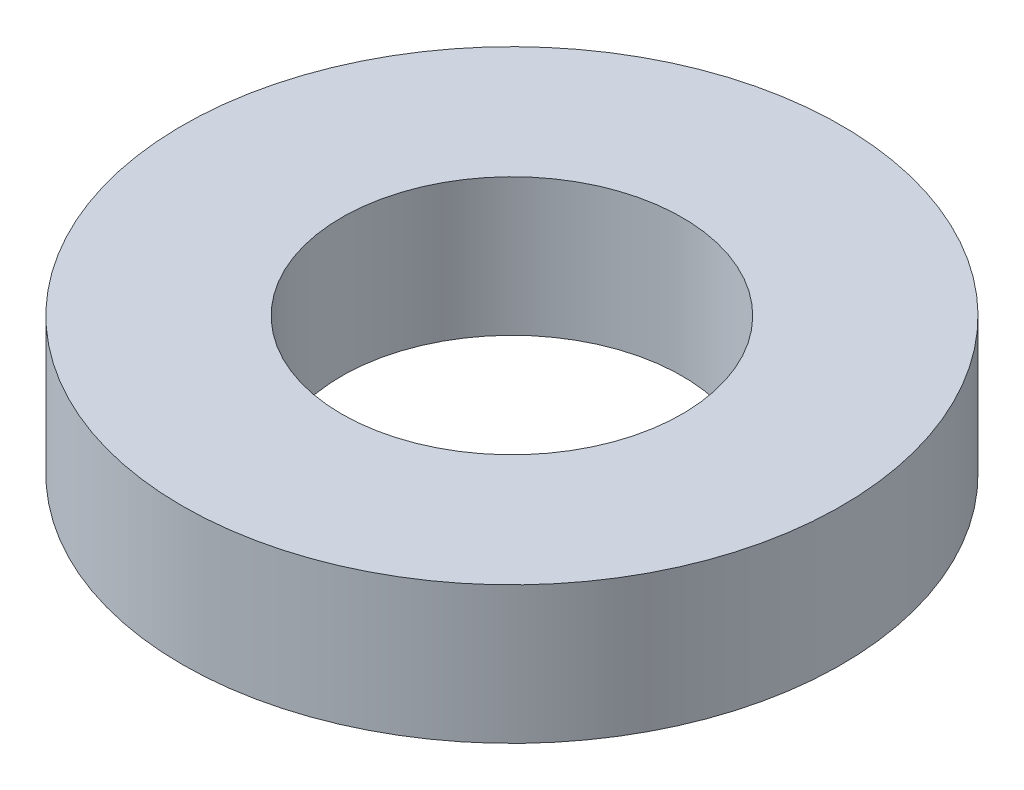
SolidWorks part; units mm, degrees
ref_plane "Front Plane" through (0, 0, 0) normal (0, 0, 1) x (1, 0, 0)
ref_plane "Top Plane" through (0, 0, 0) normal (0, 1, 0) x (1, 0, 0)
ref_plane "Right Plane" through (0, 0, 0) normal (1, 0, 0) x (0, 0, -1)
sketch "Sketch1" plane through (0, 0, 0) normal (0, 1, 0) x (1, 0, 0)
  circle A0 centre (0, 0) radius 3
  circle A1 centre (0, 0) radius 1.55
  dimension "D1" = 3.1
  dimension "D2" = 6
extrude "Boss-Extrude1" add sketch "Sketch1" along normal blind 1.25
